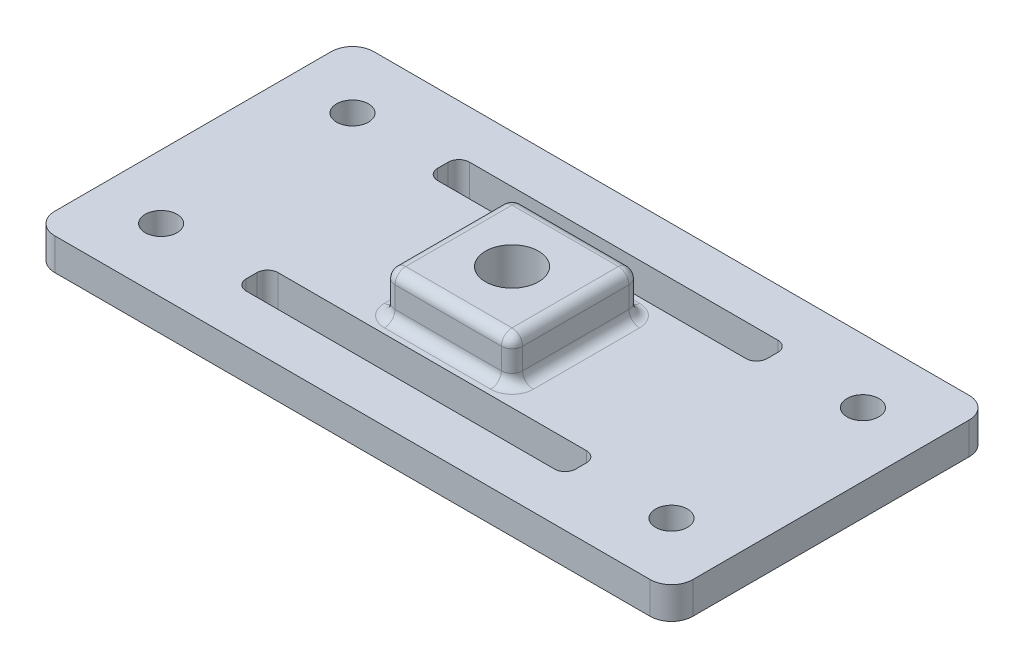
SolidWorks part; units mm, degrees
ref_plane "前视基准面" through (0, 0, 0) normal (0, 0, 1) x (1, 0, 0)
ref_plane "上视基准面" through (0, 0, 0) normal (0, 1, 0) x (1, 0, 0)
ref_plane "右视基准面" through (0, 0, 0) normal (1, 0, 0) x (0, 0, -1)
sketch "草图1" plane through (0, 0, 0) normal (0, 1, 0) x (1, 0, 0)
  line L1 (30, 15) -> (-30, 15)
  line L2 (30, 15) -> (30, -15)
  line L3 (30, -15) -> (-30, -15)
  line L4 (-30, 15) -> (-30, -15)
  line L5 (30, 15) -> (-30, -15) construction
  line L6 (30, -15) -> (-30, 15) construction
  point P0 (0, 0)
extrude "凸台-拉伸1" add sketch "草图1" along normal blind 3
sketch "草图2" plane through (0, 3, 0) normal (0, 1, 0) x (1, 0, 0)
  line L0 (-30, -9) -> (-24, -9) construction
  line L1 (-30, 15) -> (-30, -15) construction
  line L2 (-24, -9) -> (-24, -15) construction
  line L3 (-30, -15) -> (30, -15) construction
  circle A0 centre (-24, -9) radius 1.5
extrude "切除-拉伸1" cut sketch "草图2" against normal blind 3
sketch "草图5" plane through (0, 3, 0) normal (0, 1, 0) x (1, 0, 0)
  line L1 (6, 6) -> (-6, 6)
  line L2 (6, 6) -> (6, -6)
  line L3 (6, -6) -> (-6, -6)
  line L4 (-6, 6) -> (-6, -6)
  line L5 (6, 6) -> (-6, -6) construction
  line L6 (6, -6) -> (-6, 6) construction
  point P0 (0, 0)
extrude "凸台-拉伸2" add sketch "草图5" along normal blind 4
mirror "镜向1" about plane through (0, 0, 0) normal (0, 0, 1) of "切除-拉伸1"
mirror "镜向2" about plane through (0, 0, 0) normal (1, 0, 0) of "镜向1", "切除-拉伸1"
sketch "草图3" plane through (0, 3, 0) normal (0, 1, 0) x (1, 0, 0)
  line L0 (-24, -9) -> (24, -9) construction
  line L2 (15.4964, -10.5) -> (-15.4964, -10.5)
  line L3 (15.4964, -10.5) -> (15.4964, -7.5)
  line L4 (15.4964, -7.5) -> (-15.4964, -7.5)
  line L5 (-15.4964, -10.5) -> (-15.4964, -7.5)
  line L6 (15.4964, -10.5) -> (-15.4964, -7.5) construction
  line L7 (15.4964, -7.5) -> (-15.4964, -10.5) construction
  point P4 (0, -9)
extrude "切除-拉伸2" cut sketch "草图3" against normal blind 3
fillet "圆角1" radius 1 4 edges at (15.4964, 1.5, 10.5) (15.4964, 1.5, 7.5) (-15.4964, 1.5, 10.5) (-15.4964, 1.5, 7.5)
mirror "镜向3" about plane through (0, 0, 0) normal (0, 0, 1) of "圆角1", "切除-拉伸2"
fillet "圆角2" radius 2 4 edges at (-30, 1.5, -15) (30, 1.5, -15) (30, 1.5, 15) (-30, 1.5, 15)
sketch "草图4" plane through (0, 3, 0) normal (0, 1, 0) x (1, 0, 0)
  circle A0 centre (0, 0) radius 2.5
extrude "切除-拉伸3" cut sketch "草图4" against normal through all both and the other way through all
fillet "圆角3" radius 1 12 edges at (-6, 3, 0) (0, 7, -6) (6, 7, 0) (0, 7, 6) (-6, 7, 0) (0, 3, -6) (0, 3, 6) (-6, 5, -6) (-6, 5, 6) (6, 3, 0) (6, 5, 6) (6, 5, -6)
